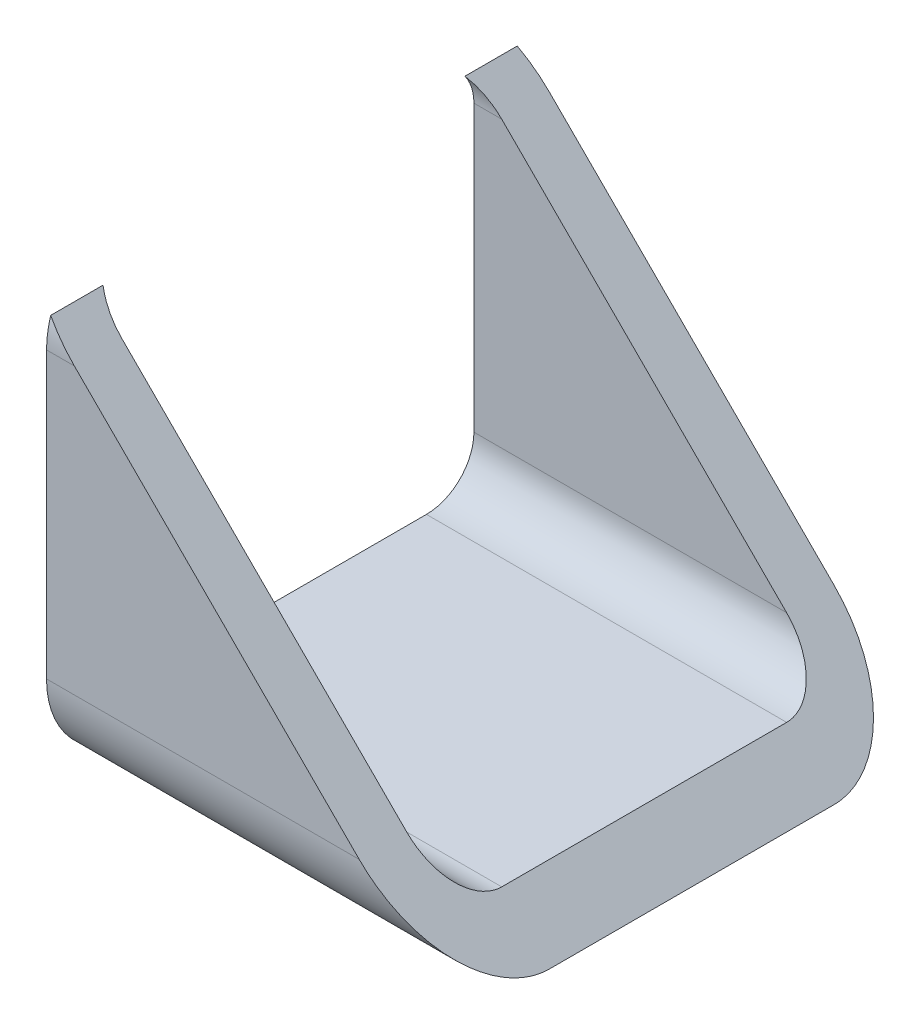
SolidWorks part; units mm, degrees
ref_plane "Alzado" through (0, 0, 0) normal (0, 0, 1) x (1, 0, 0)
ref_plane "Planta" through (0, 0, 0) normal (0, 1, 0) x (1, 0, 0)
ref_plane "Vista lateral" through (0, 0, 0) normal (1, 0, 0) x (0, 0, -1)
sketch3d "3DSketch1"
  line L0 (0, 0, 0) -> (40, 0, 0)
  dimension "D1" = 40
other "Tubo cuadrado 40 X 40 X 4(1)"
ref_plane "Plane1" through (0, 0, 0) normal (1, 0, 0) x (0, 0, -1)
sketch "Sketch6" plane through (0, 0, 0) normal (1, 0, 0) x (0, 0, -1)
  line L0 (-12, -16) -> (12, -16)
  line L1 (-16, -12) -> (-16, 12)
  line L2 (12, 16) -> (-12, 16)
  line L3 (16, 12) -> (16, -12)
  line L4 (-12, -20) -> (12, -20)
  line L5 (-20, -12) -> (-20, 12)
  line L6 (12, 20) -> (-12, 20)
  line L7 (20, 12) -> (20, -12)
  arc A0 (20, 12) -> (12, 20) centre (12, 12) ccw
  arc A1 (12, -20) -> (20, -12) centre (12, -12) ccw
  arc A2 (-20, -12) -> (-12, -20) centre (-12, -12) ccw
  arc A3 (-12, 20) -> (-20, 12) centre (-12, 12) ccw
  arc A4 (-12, 16) -> (-16, 12) centre (-12, 12) ccw
  arc A5 (16, 12) -> (12, 16) centre (12, 12) ccw
  arc A6 (12, -16) -> (16, -12) centre (12, -12) ccw
  arc A7 (-16, -12) -> (-12, -16) centre (-12, -12) ccw
  point P0 (-20, 0)
  point P1 (20, 0)
  point P2 (0, 20)
  point P3 (0, -20)
  point P4 (0, 0)
  point P5 (-20, -20)
  point P6 (20, -20)
  point P7 (20, 20)
  point P8 (-20, 20)
  point P33 (0, 0)
  dimension "D1" = 8
  dimension "Thickness" = 4
  dimension "V_leg" = 40
sketch "Sketch2" plane through (0, 0, 20) normal (0, 0, 1) x (1, 0, 0)
  line L0 (0, 20) -> (40, -20) construction
  line L3 (0, 20) -> (40, 20) construction
  line L4 (40, 20) -> (40, -20) construction
  line L5 (-9.6569, 24) -> (44, -29.6569)
  line L6 (44, 24) -> (44, -29.6569)
  line L7 (-9.6569, 24) -> (44, 24)
  dimension "D1" = 4
extrude "Extrude1" cut sketch "Sketch2" against normal up to next
